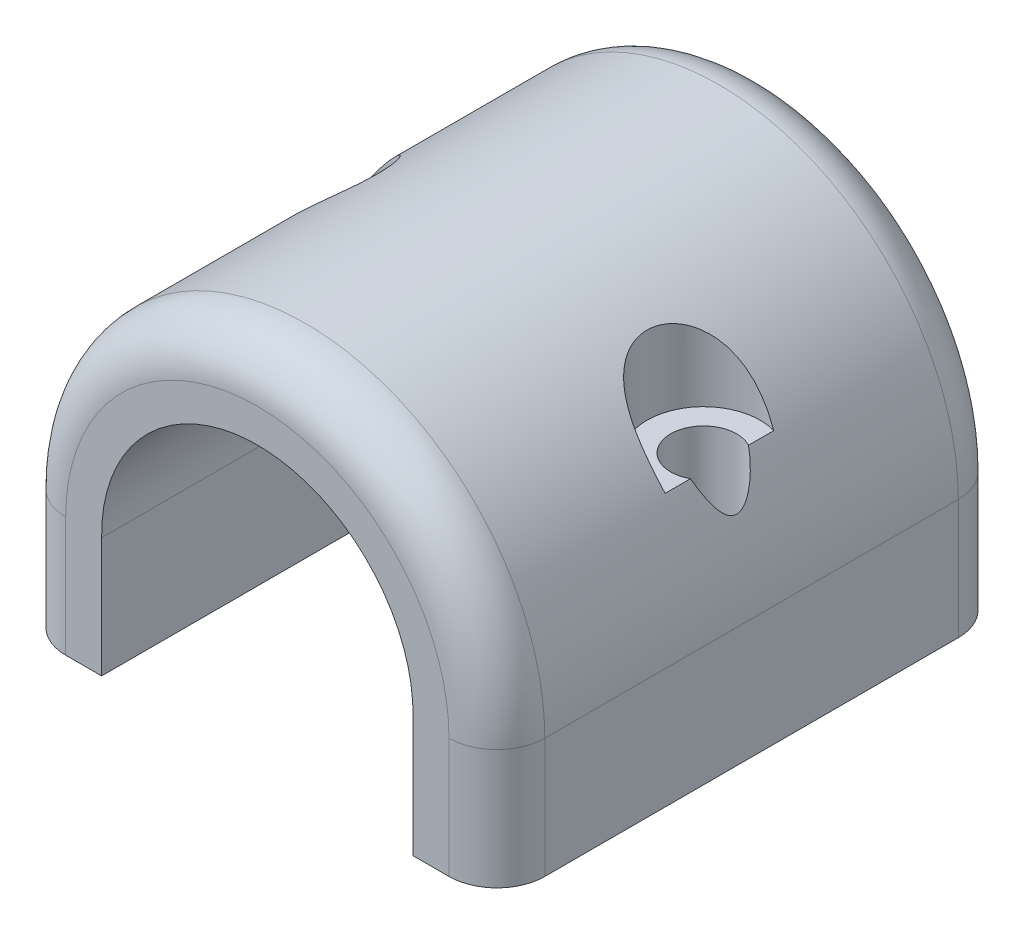
SolidWorks part; units mm, degrees
material "PLA"
ref_plane "Front Plane" through (0, 0, 0) normal (0, 0, 1) x (1, 0, 0)
ref_plane "Top Plane" through (0, 0, 0) normal (0, 1, 0) x (1, 0, 0)
ref_plane "Right Plane" through (0, 0, 0) normal (1, 0, 0) x (0, 0, -1)
sketch "Sketch1" plane through (0, 0, 0) normal (0, 1, 0) x (1, 0, 0)
  line L0 (-10.16, 0) -> (10.16, 0) construction
  line L1 (-12.7, -13.5) -> (12.7, -13.5)
  line L2 (-12.7, -13.5) -> (-12.7, 13.5)
  line L3 (-12.7, 13.5) -> (12.7, 13.5)
  line L4 (12.7, -13.5) -> (12.7, 13.5)
  line L5 (-12.7, -13.5) -> (12.7, 13.5) construction
  line L6 (-12.7, 13.5) -> (12.7, -13.5) construction
  circle A0 centre (-10.16, 0) radius 1.75
  circle A1 centre (10.16, 0) radius 1.75
  point P0 (0, 0)
  point P10 (0, 0)
  dimension "D2" = 3.5
  dimension "D1" = 25.4
  dimension "D3" = 2.54
  dimension "D4" = 27
extrude "Boss-Extrude1" add sketch "Sketch1" along normal mid plane 6.35
sketch "Sketch2" plane through (0, 0, 13.5) normal (0, 0, 1) x (1, 0, 0)
  line L0 (-12.7, 3.175) -> (12.7, 3.175) construction
  line L1 (-8.255, -3.175) -> (8.255, -3.175)
  line L2 (-8.255, -3.175) -> (-8.255, 3.175)
  line L3 (-8.255, 3.175) -> (8.255, 3.175)
  line L4 (8.255, -3.175) -> (8.255, 3.175)
  line L5 (-8.255, -3.175) -> (8.255, 3.175) construction
  line L6 (-8.255, 3.175) -> (8.255, -3.175) construction
  point P0 (0, 0)
  dimension "D1" = 16.51
extrude "Cut-Extrude1" cut sketch "Sketch2" against normal through all
sketch "Sketch3" plane through (0, 0, 13.5) normal (0, 0, 1) x (1, 0, 0)
  line L0 (-12.7, 3.175) -> (-8.255, 3.175)
  line L1 (8.255, 3.175) -> (12.7, 3.175)
  line L2 (-12.7, -3.175) -> (-8.255, -3.175) construction
  arc A0 (-8.255, 3.175) -> (8.255, 3.175) centre (0, 3.301) cw
  arc A1 (-12.7, 3.175) -> (12.7, 3.175) centre (0, 3.175) cw
  point P8 (0, 11.557)
  dimension "D1" = 14.732
extrude "Boss-Extrude2" add sketch "Sketch3" against normal through all
sketch "Sketch4" plane through (0, 3.175, 0) normal (0, -1, 0) x (1, 0, 0)
  circle A0 centre (-10.16, 0) radius 1.75
  circle A1 centre (10.16, 0) radius 1.75
  circle A2 centre (10.16, 0) radius 1.75 construction
extrude "Cut-Extrude2" cut sketch "Sketch4" against normal through all
ref_plane "Plane1" through (0, 15.875, 0) normal (0, 1, 0) x (1, 0, 0)
sketch "Sketch5" plane through (0, 15.875, 0) normal (0, 1, 0) x (1, 0, 0)
  circle A0 centre (-10.16, 0) radius 3
  circle A1 centre (10.16, 0) radius 3
  dimension "D1" = 6
extrude "Cut-Extrude3" cut sketch "Sketch5" against normal blind 6.35
fillet "Fillet1" radius 2.54 6 edges at (-12.7, 0, -13.5) (0, 15.875, 13.5) (0, 15.875, -13.5) (-12.7, 0, 13.5) (12.7, 0, -13.5) (12.7, 0, 13.5)
